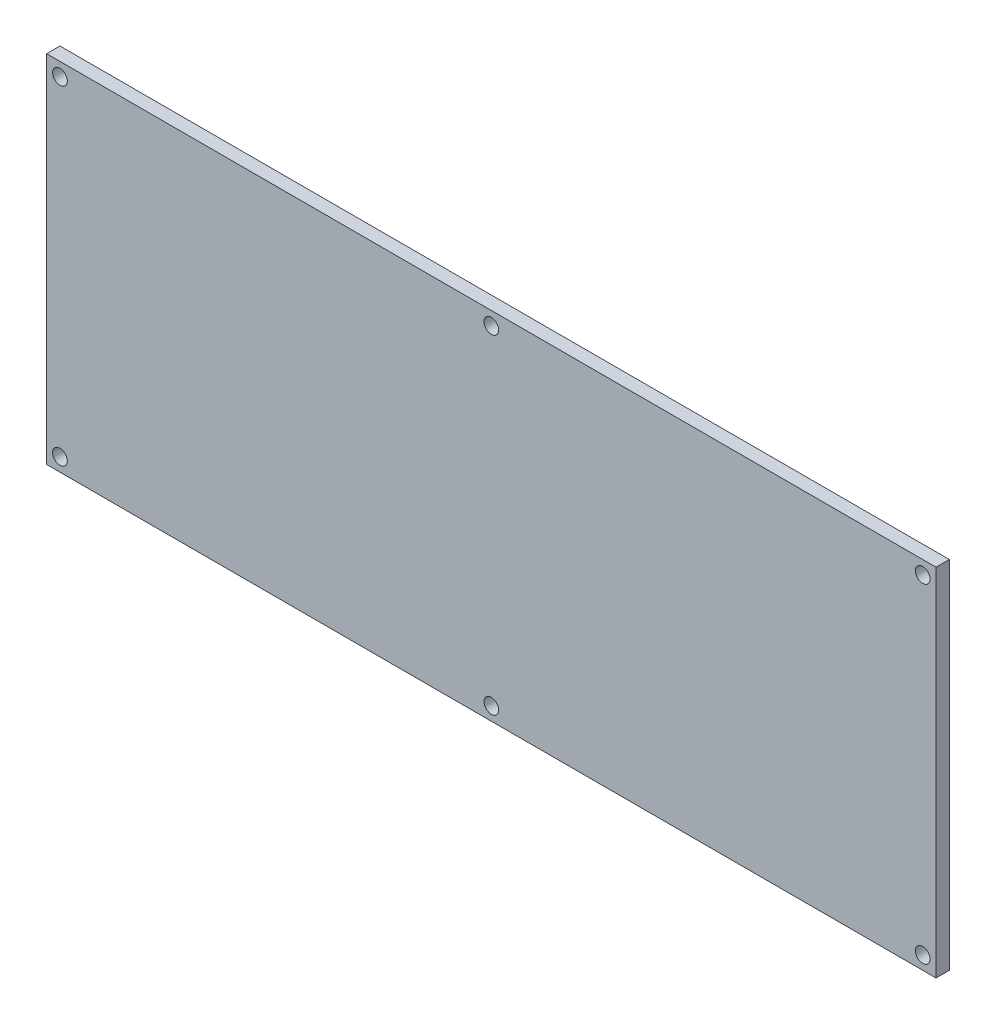
SolidWorks part; units mm, degrees
material "1060 合金"
ref_plane "前视基准面" through (0, 0, 0) normal (0, 0, 1) x (1, 0, 0)
ref_plane "上视基准面" through (0, 0, 0) normal (0, 1, 0) x (1, 0, 0)
ref_plane "右视基准面" through (0, 0, 0) normal (1, 0, 0) x (0, 0, -1)
sketch "草图1" plane through (0, 0, 0) normal (0, 0, 1) x (1, 0, 0)
  line L0 (-100, 0) -> (0, 0) construction
  line L1 (100, 40) -> (-100, 40)
  line L2 (100, 40) -> (100, -40)
  line L3 (100, -40) -> (-100, -40)
  line L4 (-100, 40) -> (-100, -40)
  line L5 (100, 40) -> (-100, -40) construction
  line L6 (100, -40) -> (-100, 40) construction
  circle A0 centre (-97, 37) radius 1.65
  circle A1 centre (0, 37) radius 1.65
  circle A2 centre (97, 37) radius 1.65
  circle A3 centre (-97, -37) radius 1.65
  circle A4 centre (0, -37) radius 1.65
  circle A5 centre (97, -37) radius 1.65
  point P0 (0, 0)
  dimension "D3" = 3.3
  dimension "D4" = 3.3
  dimension "D5" = 3.3
  dimension "D6" = 3
  dimension "D7" = 3
  dimension "D8" = 3
  dimension "D1" = 200
  dimension "D2" = 80
extrude "凸台-拉伸1" add sketch "草图1" along normal blind 3
equation "\"3。5\"=7.11047"
